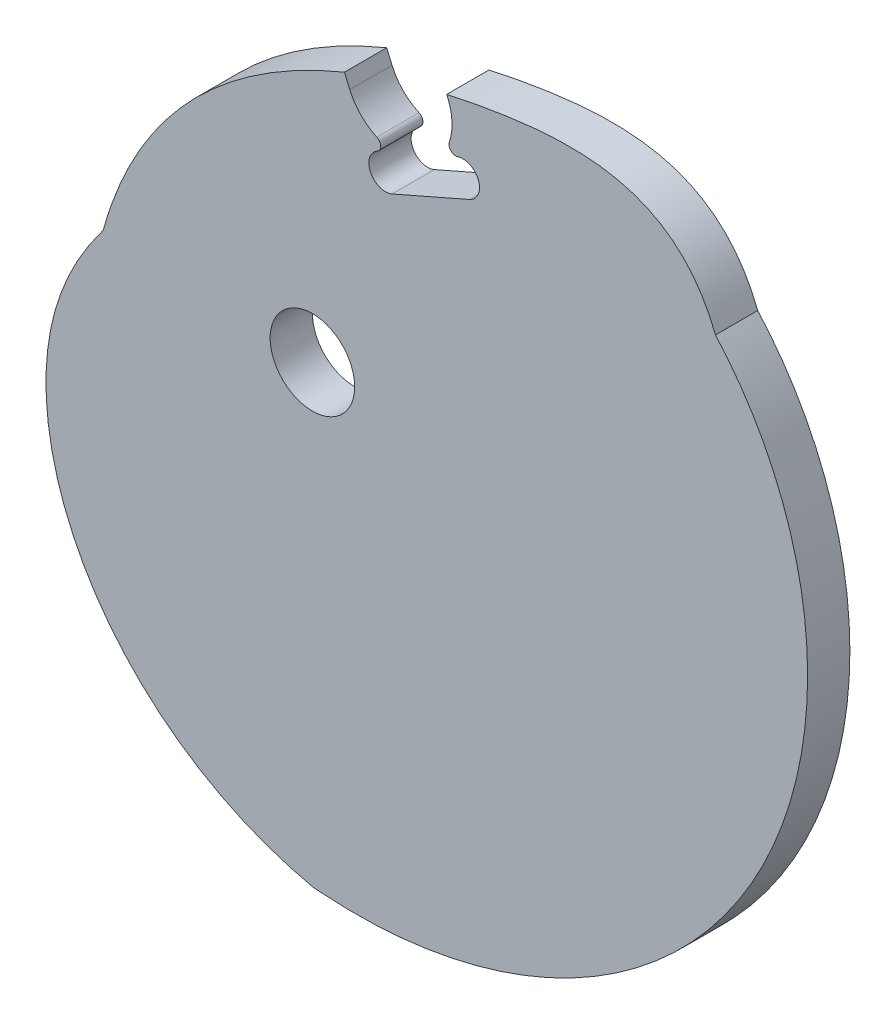
SolidWorks part; units mm, degrees
ref_plane "Front Plane" through (0, 0, 0) normal (0, 0, 1) x (1, 0, 0)
ref_plane "Top Plane" through (0, 0, 0) normal (0, 1, 0) x (1, 0, 0)
ref_plane "Right Plane" through (0, 0, 0) normal (1, 0, 0) x (0, 0, -1)
curve "Curve1"
sketch "Sketch1" plane through (0, 0, 0) normal (0, 0, 1) x (1, 0, 0)
  line L0 (10.9805, 30.1851) -> (22.6104, 35.2876) construction
  line L1 (9.976, 32.4744) -> (21.6059, 37.5769)
  line L2 (11.9849, 27.8957) -> (23.6148, 32.9983)
  line L3 (10.7688, 46.4724) -> (16.7954, 32.7363) construction
  line L4 (-15.5247, -36.542) -> (-17.0714, -47.8252) construction
  line L5 (-12.072, -37.0153) -> (-13.6188, -48.2986) construction
  line L6 (-18.9773, -36.0687) -> (-20.5241, -47.3519) construction
  line L7 (-15.1851, -34.0651) -> (-15.8642, -39.0188) construction
  line L8 (5.6152, 38.2953) -> (4.817, 40.1667)
  line L9 (20.342, 44.5764) -> (20.1797, 44.9568)
  circle A0 centre (0, 0) radius 6.35
  arc A1 (9.976, 32.4744) -> (11.9849, 27.8957) centre (10.9805, 30.1851) ccw
  arc A2 (23.6148, 32.9983) -> (21.6059, 37.5769) centre (22.6104, 35.2876) ccw
  arc A3 (5.6152, 38.2953) -> (20.342, 44.5764) centre (12.9786, 41.4359) ccw
  arc A4 (-12.072, -37.0153) -> (-18.9773, -36.0687) centre (-15.5247, -36.542) ccw construction
  arc A5 (-20.5241, -47.3519) -> (-13.6188, -48.2986) centre (-17.0714, -47.8252) ccw construction
  spline S0 degree 3 poles (60.5619, 33.8475) (54.8458, 48.446) (12.8047, 48.5556) (-23.7995, 29.1644) (-31.4349, 1.4766) knots 0 0 0 0 0.323798 1 1 1 1
  spline S1 degree 3 poles (-31.4349, 1.4766) (-31.5272, 1.3539) (-31.7543, 1.0497) (-32.1143, 0.5583) (-32.5148, -0.0021) (-32.9143, -0.5765) (-33.3119, -1.1651) (-33.7067, -1.7682) (-34.0978, -2.3859) (-34.4843, -3.0184) (-34.8652, -3.6658) (-35.2396, -4.3281) (-35.6066, -5.0053) (-35.9651, -5.6973) (-36.4332, -6.6447) (-36.8778, -7.6162) (-37.4035, -8.8658) (-37.8984, -10.156) (-38.3396, -11.4784) (-38.66, -12.5613) (-38.8837, -13.3886) (-39.0892, -14.2271) (-39.2755, -15.0762) (-39.4986, -16.2257) (-39.7269, -17.6867) (-39.918, -19.4686) (-40.0248, -21.281) (-40.0453, -23.1197) (-39.9779, -24.9807) (-39.821, -26.8594) (-39.5732, -28.7515) (-39.2334, -30.6526) (-38.8008, -32.5579) (-38.2746, -34.463) (-37.6546, -36.3631) (-36.9404, -38.2535) (-36.1322, -40.1295) (-35.2301, -41.9865) (-34.2348, -43.8195) (-33.147, -45.6241) (-31.9677, -47.3954) (-30.6982, -49.1288) (-29.3399, -50.8197) (-27.8945, -52.4636) (-26.3639, -54.056) (-24.7505, -55.5925) (-23.0564, -57.069) (-21.2844, -58.4811) (-19.4373, -59.8249) (-17.5182, -61.0964) (-15.5302, -62.2919) (-13.4768, -63.4077) (-11.3617, -64.4404) (-9.5538, -65.2277) (-8.0806, -65.8131) (-6.9608, -66.2301) (-5.8286, -66.6239) (-4.6845, -66.9947) (-3.5289, -67.3403) (-2.3631, -67.6669) (-1.1843, -67.9504) (-0.014, -68.2767) (1.195, -68.3213) (2.3889, -68.4148) (3.5889, -68.4701) (4.791, -68.5105) (5.9959, -68.5295) (7.203, -68.5287) (8.412, -68.5074) (10.4332, -68.4377) (12.8613, -68.2711) (15.6901, -67.9548) (18.1144, -67.5984) (20.5332, -67.1563) (22.9432, -66.6277) (25.3412, -66.0123) (27.7237, -65.3096) (30.0873, -64.5195) (32.4285, -63.6418) (34.7436, -62.6767) (37.029, -61.6245) (39.281, -60.4855) (41.4959, -59.2605) (43.6699, -57.9503) (45.7991, -56.5558) (47.8799, -55.0782) (49.9084, -53.519) (51.8809, -51.8798) (53.7935, -50.1623) (55.6427, -48.3686) (57.4246, -46.5008) (59.1358, -44.5613) (60.7726, -42.5528) (62.3317, -40.4781) (63.8096, -38.3402) (65.2031, -36.1423) (66.5091, -33.8878) (67.7246, -31.5803) (68.8468, -29.2235) (69.8728, -26.8215) (70.8003, -24.3784) (71.6268, -21.8985) (72.3501, -19.3862) (72.9683, -16.8461) (73.4796, -14.2831) (73.8825, -11.702) (74.1757, -9.1078) (74.358, -6.5057) (74.4286, -3.9008) (74.387, -1.2987) (74.2329, 1.2955) (73.9661, 3.8762) (73.5869, 6.4378) (73.0958, 8.9748) (72.4936, 11.4816) (71.7814, 13.9527) (70.9605, 16.3824) (70.0327, 18.7651) (68.9998, 21.0953) (67.8642, 23.3675) (66.6283, 25.5763) (65.2952, 27.7164) (63.8679, 29.7824) (62.3499, 31.7694) (61.2241, 33.1042) (60.6172, 33.7857) (60.5619, 33.8475) knots 0.746012 0.746012 0.746012 0.746012 0.747291 0.749171 0.751082 0.753022 0.754993 0.756992 0.759021 0.761077 0.76316 0.765271 0.767407 0.769569 0.771756 0.776201 0.778458 0.783036 0.787697 0.790056 0.792433 0.794828 0.797239 0.799666 0.804571 0.80954 0.814575 0.819674 0.824838 0.830066 0.835358 0.840713 0.846131 0.851612 0.857155 0.862759 0.868424 0.874149 0.879933 0.885776 0.891678 0.897636 0.903651 0.909721 0.915847 0.922026 0.928258 0.934541 0.940876 0.947261 0.953694 0.960175 0.966703 0.973276 0.976579 0.979893 0.983218 0.986554 0.9899 0.993257 0.996623 1 1.00332 1.006645 1.009976 1.013312 1.016655 1.020003 1.023357 1.026716 1.036831 1.043603 1.050399 1.057218 1.064061 1.070927 1.077816 1.084728 1.091662 1.098619 1.105597 1.112596 1.119615 1.126655 1.133714 1.140792 1.147888 1.155 1.16213 1.169275 1.176434 1.183607 1.190793 1.19799 1.205199 1.212416 1.219642 1.226875 1.234115 1.241359 1.248606 1.255856 1.263106 1.270356 1.277605 1.28485 1.29209 1.299324 1.306551 1.313769 1.320976 1.328171 1.335352 1.342519 1.349669 1.356801 1.363913 1.371004 1.378073 1.385117 1.392136 1.399128 1.406092 1.413026 1.419929 1.420619 1.420619 1.420619 1.420619
  point P6 (16.7954, 32.7363)
  point P18 (-16.298, -42.1836)
  dimension "D1" = 12.7
  dimension "D5" = 5.5
  dimension "D2" = 12.7
  dimension "D3" = 5
  dimension "D4" = 15
extrude "Boss-Extrude1" add sketch "Sketch1" along normal mid plane 6.35 contours A3 S1 A0 A2 L2 A1 L1
sketch "Sketch3" plane through (0, 0, 3.175) normal (0, 0, 1) x (1, 0, 0)
  point P0 (-13.488, -5.936)
  point P1 (-3.3675, -25.0764)
  point P3 (-25.0038, -24.2708)
fillet "Fillet3" radius 1 2 edges at (12.2346, 33.4654, 0) (19.3474, 36.586, 0)
sketch "Sketch7" [suppressed] plane through (0, 0, 0) normal (0, 0, 1) x (1, 0, 0)
  circle A0 centre (0, 0) radius 6.35
  circle A1 centre (0, 0) radius 3.175
  dimension "D1" = 6.35
sketch "Sketch8" [suppressed] plane through (0, 0, 0) normal (0, 0, 1) x (1, 0, 0)
  line L0 (10.9805, 30.1851) -> (22.6104, 35.2876) construction
  line L1 (9.976, 32.4744) -> (21.6059, 37.5769)
  line L2 (11.9849, 27.8957) -> (23.6148, 32.9983)
  circle A0 centre (12.6554, 42.1677) radius 1
  arc A1 (5.6152, 38.2953) -> (20.342, 44.5764) centre (12.9786, 41.4359) ccw construction
  circle A2 centre (0, 0) radius 6.35
  arc A3 (9.976, 32.4744) -> (11.9849, 27.8957) centre (10.9805, 30.1851) ccw
  arc A4 (23.6148, 32.9983) -> (21.6059, 37.5769) centre (22.6104, 35.2876) ccw
  arc A5 (23.6148, 32.9983) -> (21.6059, 37.5769) centre (22.6104, 35.2876) ccw construction
  point P12 (16.7954, 32.7363)
  dimension "D2" = 2
  dimension "D1" = 0.8
sketch "Sketch15" plane through (0, 0, 3.175) normal (0, 0, 1) x (1, 0, 0)
  circle A0 centre (-43.3531, -41.4597) radius 1.1
  circle A1 centre (13.5262, -74.2009) radius 1.1
  dimension "D1" = 2.2
  dimension "D2" = 2.2
sketch "Sketch16" plane through (0, 0, 3.175) normal (0, 0, 1) x (1, 0, 0)
  circle A0 centre (-5.523, -52.2474) radius 1.05
  circle A1 centre (5.4449, -44.5935) radius 1.05
  circle A2 centre (10.1611, -19.1035) radius 1.1 construction
  circle A3 centre (-5.523, -52.2474) radius 1.05 construction
  circle A4 centre (5.4449, -44.5935) radius 1.05 construction
  circle A5 centre (10.1611, -19.1035) radius 1.1 construction
sketch "Sketch18" plane through (0, 0, 3.175) normal (0, 0, 1) x (1, 0, 0)
  circle A0 centre (-12.5246, -41.0492) radius 0.7
  circle A1 centre (0, -39.819) radius 0.7
  dimension "D1" = 1.4
  dimension "D2" = 1.4
